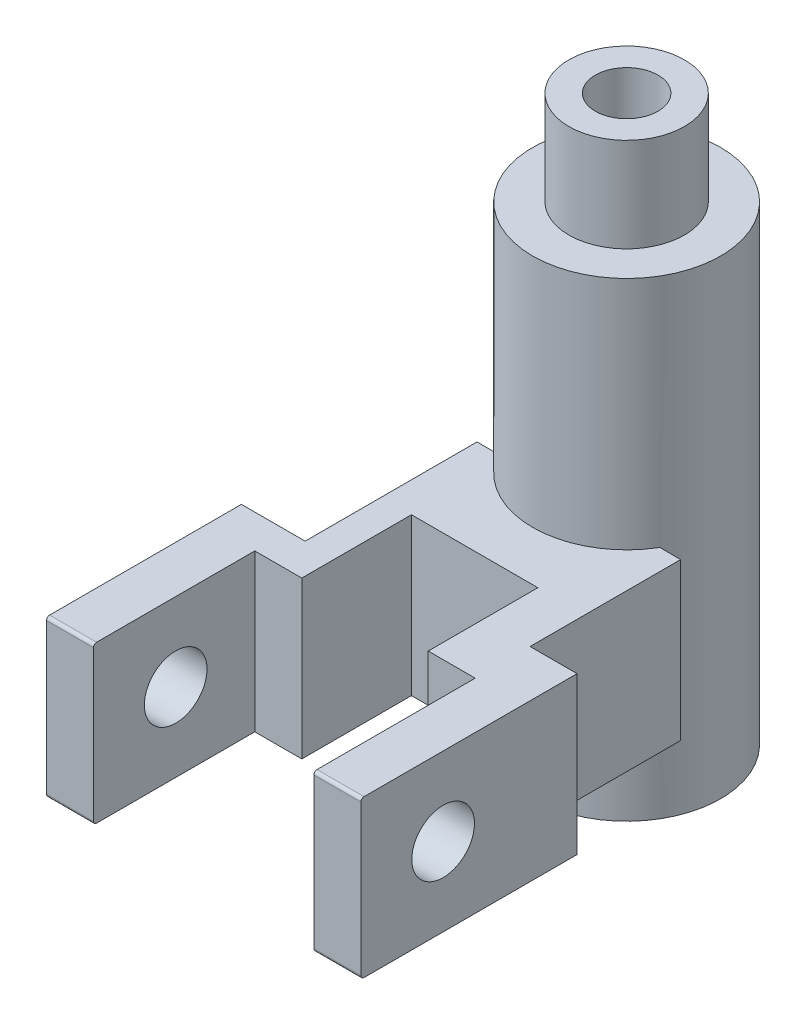
SolidWorks part; units mm, degrees
ref_plane "Front Plane" through (0, 0, 0) normal (0, 0, 1) x (1, 0, 0)
ref_plane "Top Plane" through (0, 0, 0) normal (0, 1, 0) x (1, 0, 0)
ref_plane "Right Plane" through (0, 0, 0) normal (1, 0, 0) x (0, 0, -1)
sketch "Sketch1" plane through (0, 0, 0) normal (0, 1, 0) x (1, 0, 0)
  line L0 (-42.4859, 40.678) -> (-42.4859, -8.2768)
  line L1 (-42.4859, -8.2768) -> (-62.8249, -8.2768)
  line L2 (-62.8249, -8.2768) -> (-62.8249, -39.0113)
  line L5 (-47.8249, -19.0113) -> (-32.8249, -19.0113)
  line L6 (-32.8249, -19.0113) -> (-32.8249, 15.9887)
  line L7 (-32.8249, 15.9887) -> (7.5141, 15.9887)
  line L8 (7.5141, 15.9887) -> (7.5141, -19.0113)
  line L9 (7.5141, -19.0113) -> (22.5141, -19.0113)
  line L13 (22.5141, 46.5537) -> (-42.4859, 46.5537)
  line L14 (-42.4859, 46.5537) -> (-42.4859, 40.678)
  line L15 (-62.8249, -39.0113) -> (-62.8249, -70.4843)
  line L16 (-62.8249, -70.4843) -> (-47.8249, -70.4843)
  line L17 (-47.8249, -70.4843) -> (-47.8249, -19.0113)
  line L18 (37.5141, -39.0113) -> (37.5141, -70.4843)
  line L19 (37.5141, -70.4843) -> (22.5141, -70.4843)
  line L20 (22.5141, -70.4843) -> (22.5141, -19.0113)
  line L21 (37.5141, -39.0113) -> (37.5141, -1.5113)
  line L22 (37.5141, -1.5113) -> (22.5141, -1.5113)
  line L23 (22.5141, -1.5113) -> (22.5141, 46.5537)
  dimension "D2" = 35
  dimension "D3" = 15
extrude "Boss-Extrude1" add sketch "Sketch1" along normal blind 50
sketch "Sketch2" plane through (0, 50, 0) normal (0, 1, 0) x (1, 0, 0)
  line L0 (-9.9859, 46.5537) -> (-9.9859, 61.8104) construction
  line L1 (22.5141, 46.5537) -> (-42.4859, 46.5537) construction
  circle A0 centre (-9.9859, 61.8104) radius 30
  dimension "D1" = 60
extrude "Boss-Extrude2" add sketch "Sketch2" along normal mid plane 150
sketch "Sketch3" plane through (0, 125, 0) normal (0, 1, 0) x (1, 0, 0)
  line L0 (-9.9859, 31.8104) -> (-9.9859, 61.8104) construction
  arc A0 (-35.8167, 46.5537) -> (15.845, 46.5537) centre (-9.9859, 61.8104) ccw construction
  circle A1 centre (-9.9859, 61.8104) radius 18.436
extrude "Boss-Extrude3" add sketch "Sketch3" along normal blind 30
sketch "Sketch4" plane through (0, 155, 0) normal (0, 1, 0) x (1, 0, 0)
  circle A0 centre (-9.9859, 61.8104) radius 10
  dimension "D1" = 20
extrude "Cut-Extrude1" cut sketch "Sketch4" against normal blind 220
fillet "Fillet1" radius 1 4 edges at (-55.3249, 0, 70.4843) (30.0141, 0, 70.4843) (30.0141, 50, 70.4843) (-55.3249, 50, 70.4843)
sketch "Sketch6" plane through (-47.8249, 0, 0) normal (1, 0, 0) x (0, 0, -1)
  line L0 (-44.2478, 50) -> (-44.2478, 0) construction
  line L1 (-69.4843, 50) -> (-19.0113, 50) construction
  line L2 (-69.4843, 0) -> (-19.0113, 0) construction
  circle A0 centre (-44.2478, 25) radius 10
  dimension "D1" = 20
extrude "Cut-Extrude3" cut sketch "Sketch6" against normal mid plane 220
